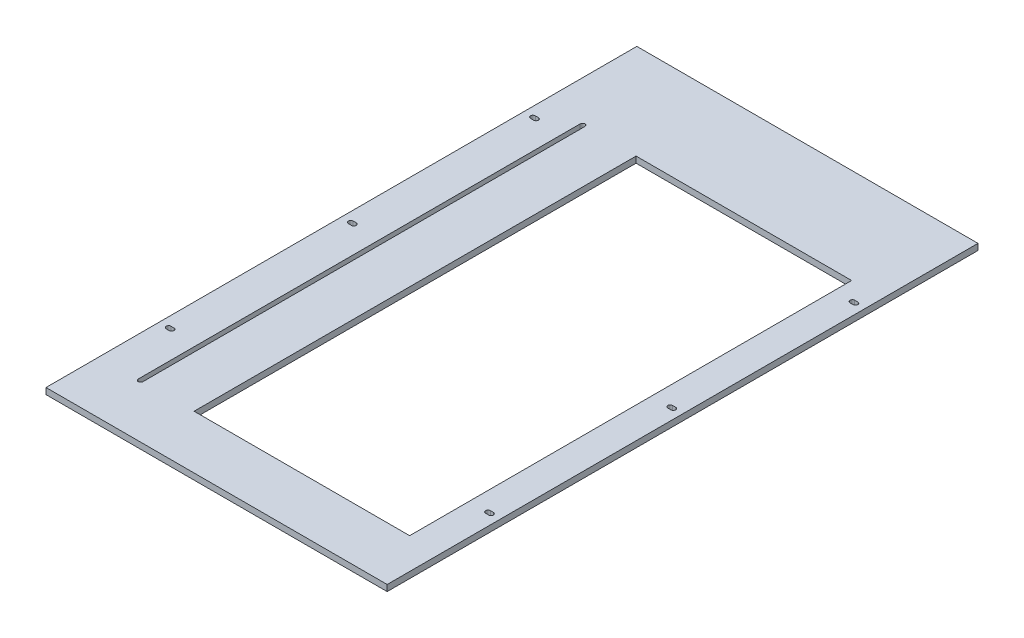
SolidWorks part; units mm, degrees
ref_plane "前基準面" through (0, 0, 0) normal (0, 0, 1) x (1, 0, 0)
ref_plane "上基準面" through (0, 0, 0) normal (0, 1, 0) x (1, 0, 0)
ref_plane "右基準面" through (0, 0, 0) normal (1, 0, 0) x (0, 0, -1)
ref_plane "平面1" through (0, -4, 0) normal (0, -1, 0) x (1, 0, 0)
sketch "草圖1" plane through (0, -4, 0) normal (0, -1, 0) x (1, 0, 0)
  line L0 (-113.7553, 186.9784) -> (-113.7553, -194.0216)
  line L1 (-113.7553, -194.0216) -> (106.2447, -194.0216)
  line L2 (106.2447, -194.0216) -> (106.2447, 186.9784)
  line L3 (106.2447, 186.9784) -> (-113.7553, 186.9784)
  line L4 (-85.7553, 152.4784) -> (-85.7553, -132.5216)
  line L5 (-88.7553, -132.5216) -> (-88.7553, 152.4784)
  line L6 (-105.7553, -122.5216) -> (-107.7553, -122.5216)
  line L7 (-107.7553, -119.5216) -> (-105.7553, -119.5216)
  line L8 (98.2447, 115.4784) -> (100.2447, 115.4784)
  line L9 (100.2447, 112.4784) -> (98.2447, 112.4784)
  line L10 (98.2447, -2.0216) -> (100.2447, -2.0216)
  line L11 (100.2447, -5.0216) -> (98.2447, -5.0216)
  line L12 (-107.7553, -2.0216) -> (-105.7553, -2.0216)
  line L13 (-105.7553, -5.0216) -> (-107.7553, -5.0216)
  line L14 (-107.7553, 115.4784) -> (-105.7553, 115.4784)
  line L15 (-105.7553, 112.4784) -> (-107.7553, 112.4784)
  line L16 (98.2447, -119.5216) -> (100.2447, -119.5216)
  line L17 (100.2447, -122.5216) -> (98.2447, -122.5216)
  line L18 (86.2447, -132.5216) -> (-52.7553, -132.5216)
  line L19 (-52.7553, -132.5216) -> (-52.7553, 152.4784)
  line L20 (-52.7553, 152.4784) -> (86.2447, 152.4784)
  line L21 (86.2447, 152.4784) -> (86.2447, -132.5216)
  arc A0 (-85.7553, -132.5216) -> (-88.7553, -132.5216) centre (-87.2553, -132.5216) cw
  arc A1 (-88.7553, 152.4784) -> (-85.7553, 152.4784) centre (-87.2553, 152.4784) cw
  arc A2 (-107.7553, -122.5216) -> (-107.7553, -119.5216) centre (-107.7553, -121.0216) cw
  arc A3 (-105.7553, -119.5216) -> (-105.7553, -122.5216) centre (-105.7553, -121.0216) cw
  arc A4 (98.2447, 112.4784) -> (98.2447, 115.4784) centre (98.2447, 113.9784) cw
  arc A5 (100.2447, 115.4784) -> (100.2447, 112.4784) centre (100.2447, 113.9784) cw
  arc A6 (98.2447, -5.0216) -> (98.2447, -2.0216) centre (98.2447, -3.5216) cw
  arc A7 (100.2447, -2.0216) -> (100.2447, -5.0216) centre (100.2447, -3.5216) cw
  arc A8 (-107.7553, -5.0216) -> (-107.7553, -2.0216) centre (-107.7553, -3.5216) cw
  arc A9 (-105.7553, -2.0216) -> (-105.7553, -5.0216) centre (-105.7553, -3.5216) cw
  arc A10 (-107.7553, 112.4784) -> (-107.7553, 115.4784) centre (-107.7553, 113.9784) cw
  arc A11 (-105.7553, 115.4784) -> (-105.7553, 112.4784) centre (-105.7553, 113.9784) cw
  arc A12 (98.2447, -122.5216) -> (98.2447, -119.5216) centre (98.2447, -121.0216) cw
  arc A13 (100.2447, -119.5216) -> (100.2447, -122.5216) centre (100.2447, -121.0216) cw
extrude "填料-伸長1" add sketch "草圖1" against normal blind 4
